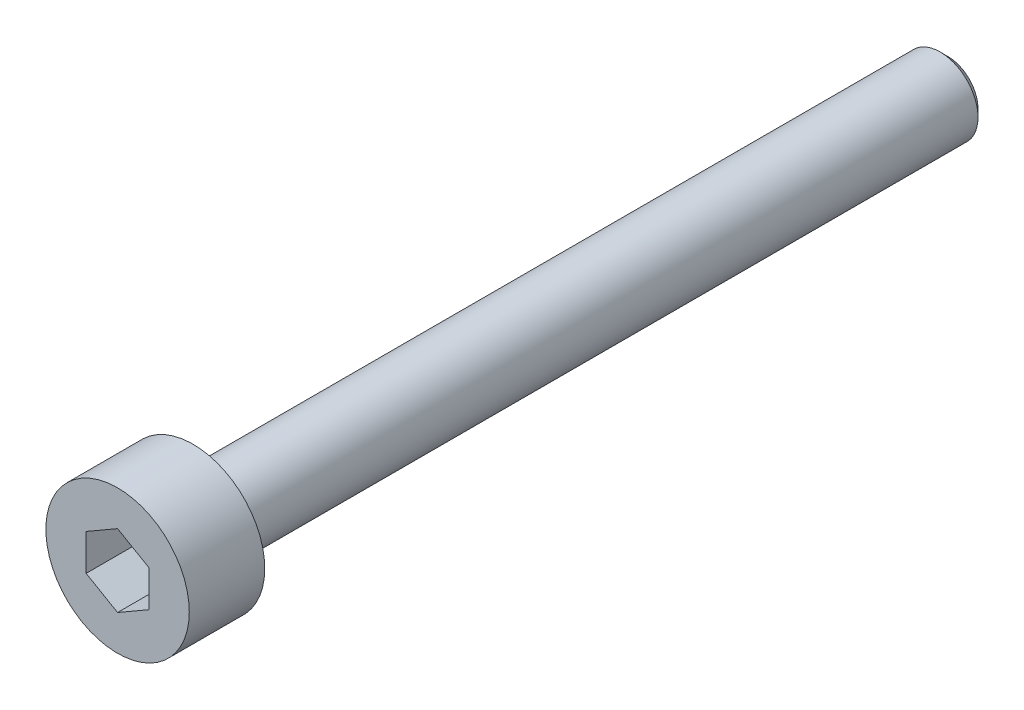
SolidWorks part; units mm, degrees
ref_plane "Front Plane" through (0, 0, 0) normal (0, 0, 1) x (1, 0, 0)
ref_plane "Top Plane" through (0, 0, 0) normal (0, 1, 0) x (1, 0, 0)
ref_plane "Right Plane" through (0, 0, 0) normal (1, 0, 0) x (0, 0, -1)
sketch "Sketch1" plane through (0, 0, 0) normal (0, 0, 1) x (1, 0, 0)
  circle A0 centre (0, 0) radius 2.85
  dimension "D1" = 5.7
extrude "Boss-Extrude1" add sketch "Sketch1" along normal blind 3
sketch "Sketch2" plane through (0, 0, 0) normal (0, 0, -1) x (-1, 0, 0)
  circle A0 centre (0, 0) radius 1.5
  dimension "D1" = 3
extrude "Boss-Extrude2" add sketch "Sketch2" along normal blind 30
chamfer "Chamfer1" distance 0.3 angle 45 1 edges at (-1.5, 0, -30)
sketch "Sketch3" plane through (0, 0, 3) normal (0, 0, 1) x (1, 0, 0)
  line L1 (0, 1.4434) -> (-1.25, 0.7217)
  line L2 (-1.25, 0.7217) -> (-1.25, -0.7217)
  line L3 (-1.25, -0.7217) -> (0, -1.4434)
  line L4 (0, -1.4434) -> (1.25, -0.7217)
  line L5 (1.25, -0.7217) -> (1.25, 0.7217)
  line L6 (1.25, 0.7217) -> (0, 1.4434)
  circle A0 centre (0, 0) radius 1.25 construction
  dimension "D1" = 2.5
extrude "Cut-Extrude1" cut sketch "Sketch3" against normal blind 2
